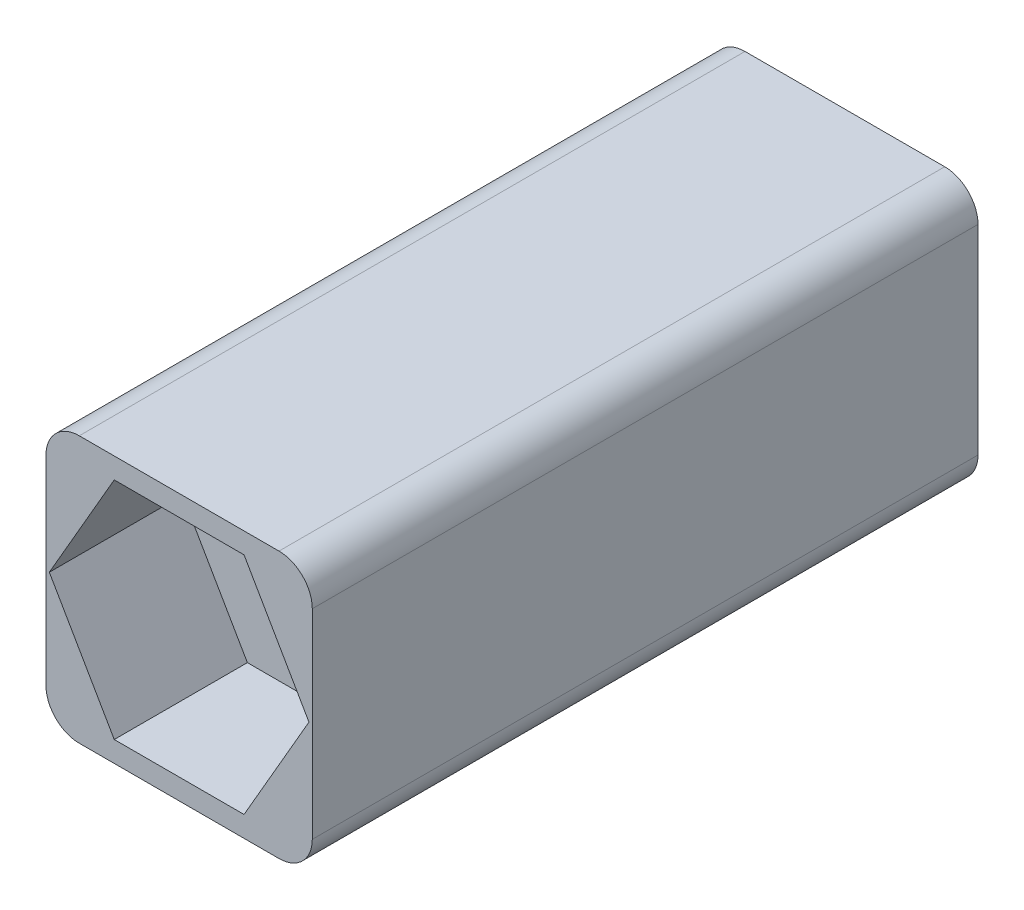
SolidWorks part; units mm, degrees
ref_plane "Front Plane" through (0, 0, 0) normal (0, 0, 1) x (1, 0, 0)
ref_plane "Top Plane" through (0, 0, 0) normal (0, 1, 0) x (1, 0, 0)
ref_plane "Right Plane" through (0, 0, 0) normal (1, 0, 0) x (0, 0, -1)
sketch "Sketch1" plane through (0, 0, 0) normal (0, 0, 1) x (1, 0, 0)
  line L1 (-2.6009, 4.6589) -> (5.3991, 4.6589)
  line L2 (-2.6009, 4.6589) -> (-2.6009, -3.3411)
  line L3 (-2.6009, -3.3411) -> (5.3991, -3.3411)
  line L4 (5.3991, 4.6589) -> (5.3991, -3.3411)
  dimension "D1" = 8
  dimension "D2" = 8
extrude "Boss-Extrude1" add sketch "Sketch1" along normal blind 20
sketch "Sketch4" plane through (0, 0, 20) normal (0, 0, 1) x (1, 0, 0)
  line L0 (-2.6009, 4.6589) -> (5.3991, -3.3411)
  circle A0 centre (1.3991, 0.6589) radius 2
extrude "Cut-Extrude1" cut sketch "Sketch4" against normal blind 20 contours L0 A0 | L0 A0
sketch "Sketch5" plane through (0, 0, 20) normal (0, 0, 1) x (1, 0, 0)
  line L0 (-2.6009, 4.6589) -> (5.3991, -3.3411)
  line L2 (-2.5009, 0.6589) -> (-0.5509, -2.7186)
  line L3 (-0.5509, -2.7186) -> (3.3491, -2.7186)
  line L4 (3.3491, -2.7186) -> (5.2991, 0.6589)
  line L5 (5.2991, 0.6589) -> (3.3491, 4.0364)
  line L6 (3.3491, 4.0364) -> (-0.5509, 4.0364)
  line L7 (-0.5509, 4.0364) -> (-2.5009, 0.6589)
  circle A0 centre (1.3991, 0.6589) radius 3.3775 construction
  dimension "D1" = 3.9
extrude "Cut-Extrude8" cut sketch "Sketch5" against normal blind 4 contours L6 L7 L0 L4 L5 | L0 L7 L2 L3 L4 L6
fillet "Fillet1" radius 1 3 edges at (5.3991, -3.3411, 10) (5.3991, 4.6589, 10) (-2.6009, 4.6589, 10)
fillet "Fillet2" radius 1 1 edges at (-2.6009, -3.3411, 10)
